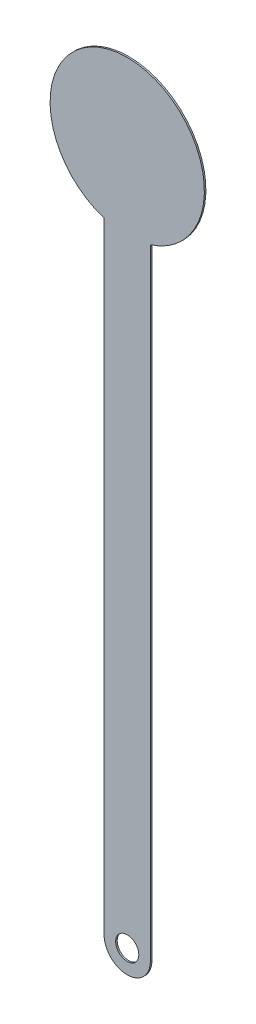
SolidWorks part; units mm, degrees
ref_plane "前视基准面" through (0, 0, 0) normal (0, 0, 1) x (1, 0, 0)
ref_plane "上视基准面" through (0, 0, 0) normal (0, 1, 0) x (1, 0, 0)
ref_plane "右视基准面" through (0, 0, 0) normal (1, 0, 0) x (0, 0, -1)
sketch "草图1" plane through (0, 0, 0) normal (0, 0, 1) x (1, 0, 0)
  line L0 (0, 0) -> (0, -42) construction
  line L1 (1.5, -4.7697) -> (1.5, -45)
  line L2 (-1.5, -4.7697) -> (-1.5, -45)
  line L4 (-1.5, 0) -> (-1.5, -42) construction
  line L5 (0, 0) -> (0, -42) construction
  line L6 (1.5, 0) -> (1.5, -42) construction
  arc A0 (1.5, -4.7697) -> (-1.5, -4.7697) centre (0, 0) ccw
  circle A1 centre (0, -45) radius 0.75
  arc A2 (-1.5, -45) -> (1.5, -45) centre (0, -45) ccw
  dimension "D1" = 1.5
  dimension "D4" = 5
  dimension "D5" = 1.5
  dimension "D3" = 45
extrude "凸台-拉伸1" add sketch "草图1" along normal blind 0.1
